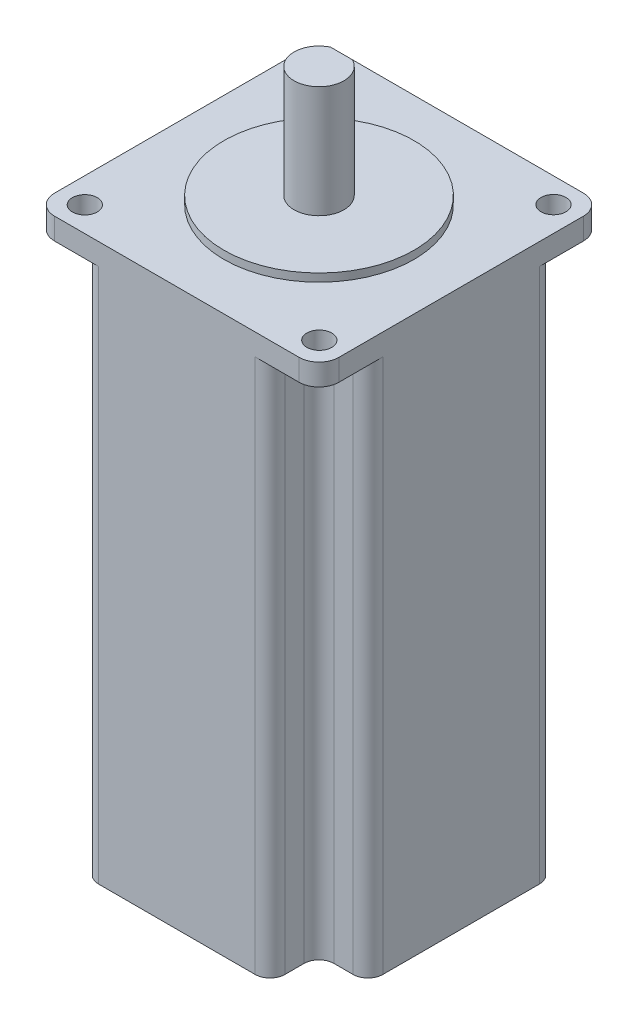
SolidWorks part; units mm, degrees
ref_plane "Front Plane" through (0, 0, 0) normal (0, 0, 1) x (1, 0, 0)
ref_plane "Top Plane" through (0, 0, 0) normal (0, 1, 0) x (1, 0, 0)
ref_plane "Right Plane" through (0, 0, 0) normal (1, 0, 0) x (0, 0, -1)
sketch "Sketch1" plane through (0, 0, 0) normal (0, 1, 0) x (1, 0, 0)
  line L1 (-24.5, -28.5) -> (24.5, -28.5)
  line L2 (-28.5, -24.5) -> (-28.5, 24.5)
  line L3 (-24.5, 28.5) -> (24.5, 28.5)
  line L4 (28.5, -24.5) -> (28.5, 24.5)
  line L5 (-28.5, -28.5) -> (28.5, 28.5) construction
  line L6 (-28.5, 28.5) -> (28.5, -28.5) construction
  arc A0 (-24.5, -28.5) -> (-28.5, -24.5) centre (-24.5, -24.5) cw
  arc A1 (24.5, -28.5) -> (28.5, -24.5) centre (24.5, -24.5) ccw
  arc A2 (24.5, 28.5) -> (28.5, 24.5) centre (24.5, 24.5) cw
  arc A3 (-24.5, 28.5) -> (-28.5, 24.5) centre (-24.5, 24.5) ccw
  point P0 (0, 0)
  dimension "D3" = 4
  dimension "D1" = 57
  dimension "D2" = 57
extrude "Boss-Extrude1" add sketch "Sketch1" along normal blind 111.53
sketch "Sketch2" plane through (0, 111.53, 0) normal (0, 1, 0) x (1, 0, 0)
  circle A0 centre (0, 0) radius 19.05
  dimension "D1" = 38.1
extrude "Boss-Extrude2" add sketch "Sketch2" along normal blind 1.6
sketch "Sketch3" plane through (0, 113.13, 0) normal (0, 1, 0) x (1, 0, 0)
  circle A0 centre (0, 0) radius 5
  dimension "D1" = 10
extrude "Boss-Extrude3" add sketch "Sketch3" along normal blind 22.4
sketch "Sketch5" plane through (0, 0, 0) normal (0, -1, 0) x (1, 0, 0)
  line L1 (-28.5, -28.5) -> (28.5, -28.5)
  line L2 (-28.5, -28.5) -> (-28.5, 28.5)
  line L3 (-28.5, 28.5) -> (28.5, 28.5)
  line L4 (28.5, -28.5) -> (28.5, 28.5)
  line L5 (-28.5, -28.5) -> (28.5, 28.5) construction
  line L6 (-28.5, 28.5) -> (28.5, -28.5) construction
  line L7 (-28.5, 28.5) -> (-18.6831, 28.5)
  line L8 (-28.5, 28.5) -> (-28.5, 18.6831)
  line L9 (-28.5, 18.6831) -> (-18.6831, 18.6831)
  line L10 (-18.6831, 28.5) -> (-18.6831, 18.6831)
  line L11 (28.5, 28.5) -> (19.6135, 28.5)
  line L12 (28.5, 28.5) -> (28.5, 19.6135)
  line L13 (28.5, 19.6135) -> (19.6135, 19.6135)
  line L14 (19.6135, 28.5) -> (19.6135, 19.6135)
  line L15 (28.5, -28.5) -> (18.6831, -28.5)
  line L16 (28.5, -28.5) -> (28.5, -18.6831)
  line L17 (28.5, -18.6831) -> (18.6831, -18.6831)
  line L18 (18.6831, -28.5) -> (18.6831, -18.6831)
  line L19 (-28.5, -28.5) -> (-18.6831, -28.5)
  line L20 (-28.5, -28.5) -> (-28.5, -18.6831)
  line L21 (-28.5, -18.6831) -> (-18.6831, -18.6831)
  line L22 (-18.6831, -28.5) -> (-18.6831, -18.6831)
  point P0 (0, 0)
  arc M19 (-24.5, 28.5) -> (-28.5, 24.5) centre (-24.5, 24.5) ccw
  line M20 (-28.5, 24.5) -> (-28.5, -24.5)
extrude "Cut-Extrude2" cut sketch "Sketch5" against normal blind 107.2 contours L10 L3 L9 M19 M20
mirror "Mirror1" about plane through (0, 0, 0) normal (1, 0, 0) of "Cut-Extrude2"
mirror "Mirror2" about plane through (0, 0, 0) normal (0, 0, 1) of "Mirror1", "Cut-Extrude2"
fillet "Fillet1" radius 3 12 edges at (-18.6831, 53.6, -18.6831) (-18.6831, 53.6, 18.6831) (18.6831, 53.6, 18.6831) (28.5, 53.6, -18.6831) (18.6831, 53.6, -18.6831) (18.6831, 53.6, -28.5) (-18.6831, 53.6, -28.5) (-28.5, 53.6, -18.6831) (-18.6831, 53.6, 28.5) (-28.5, 53.6, 18.6831) (28.5, 53.6, 18.6831) (18.6831, 53.6, 28.5)
sketch "Sketch6" plane through (0, 111.53, 0) normal (0, 1, 0) x (1, 0, 0)
  circle A0 centre (23.5, 23.5) radius 2.5
  circle A1 centre (23.5644, -23.5) radius 2.5
  circle A2 centre (-23.5, 23.5) radius 2.5
  circle A3 centre (-23.4356, -23.5) radius 2.5
  dimension "D8" = 5
  dimension "D9" = 5
  dimension "D10" = 5
  dimension "D11" = 5
  dimension "D1" = 47
  dimension "D2" = 23.5
  dimension "D3" = 47
  dimension "D4" = 47
  dimension "D5" = 47
  dimension "D6" = 23.5
  dimension "D7" = 23.5
extrude "Cut-Extrude3" cut sketch "Sketch6" against normal blind 107.2
sketch "Sketch9" plane through (0, 135.53, 0) normal (0, 1, 0) x (1, 0, 0)
  line L1 (0, 4.5) -> (2.1794, 4.5)
  line L2 (0, 4.5) -> (-2.1794, 4.5)
  arc A0 (2.1794, 4.5) -> (-2.1794, 4.5) centre (0, 0) ccw
  circle A1 centre (0, 0) radius 5 construction
extrude "Cut-Extrude4" cut sketch "Sketch9" against normal blind 20
